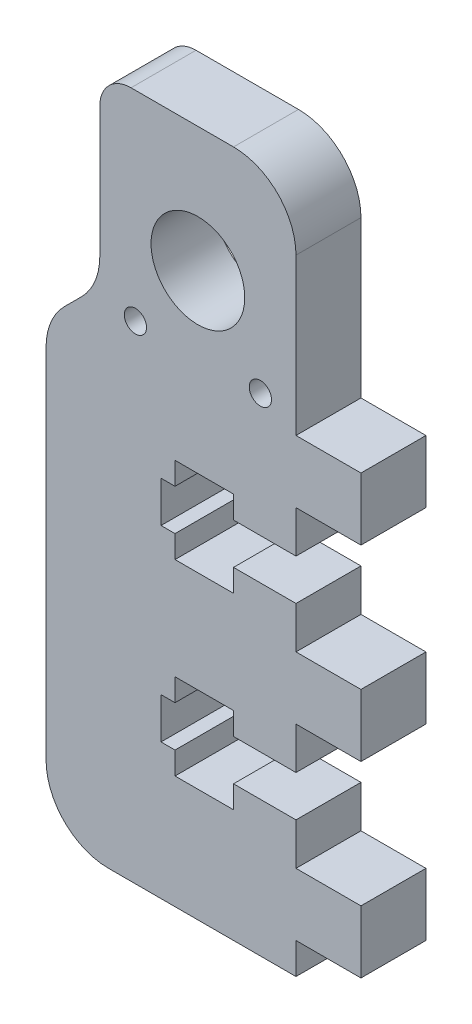
SolidWorks part; units mm, degrees
material "Acrylic (Blue)"
ref_plane "Front Plane" through (0, 0, 0) normal (0, 0, 1) x (1, 0, 0)
ref_plane "Top Plane" through (0, 0, 0) normal (0, 1, 0) x (1, 0, 0)
ref_plane "Right Plane" through (0, 0, 0) normal (1, 0, 0) x (0, 0, -1)
sketch "Sketch1" plane through (0, 0, 0) normal (0, 0, 1) x (1, 0, 0)
  line L0 (0, 0) -> (0, 69.85)
  line L1 (-9.9695, 57.15) -> (-9.9695, 129.438) construction
  line L2 (-19.939, 69.85) -> (0, 69.85)
  line L3 (0, 0) -> (-25.4, 0)
  line L4 (-25.4, 0) -> (-25.4, 45.339)
  line L6 (-19.939, 50.8) -> (-19.939, 69.85)
  line L7 (-19.939, 50.8) -> (-25.4, 45.339)
  circle A0 centre (-9.9695, 57.15) radius 4.7625
  circle A3 centre (-9.9695, 57.15) radius 8.6995 construction
  line B0 (0, 37.0078) -> (-6.35, 37.0078) construction
  line B1 (-6.35, 37.0078) -> (-6.35, 39.2938) construction
  line B2 (-6.35, 39.2938) -> (-12.2936, 39.2938) construction
  line B3 (-12.2936, 39.2938) -> (-12.2936, 37.0078) construction
  line B4 (-12.2936, 37.0078) -> (-13.716, 37.0078) construction
  line B5 (-13.716, 37.0078) -> (-13.716, 32.8422) construction
  line B6 (-13.716, 32.8422) -> (-12.2936, 32.8422) construction
  line B7 (-12.2936, 32.8422) -> (-12.2936, 30.5562) construction
  line B8 (-12.2936, 30.5562) -> (-6.35, 30.5562) construction
  line B9 (-6.35, 30.5562) -> (-6.35, 32.8422) construction
  line B10 (-6.35, 32.8422) -> (0, 32.8422) construction
  line B11 (0, 28.575) -> (6.604, 28.575) construction
  line B12 (6.604, 28.575) -> (6.604, 22.225) construction
  line B13 (6.604, 22.225) -> (0, 22.225) construction
  line B14 (0, 41.275) -> (6.604, 41.275) construction
  line B15 (6.604, 41.275) -> (6.604, 47.625) construction
  line B16 (6.604, 47.625) -> (0, 47.625) construction
  line B17 (6.604, 3.175) -> (0, 3.175) construction
  line B18 (0, 17.9578) -> (-6.35, 17.9578) construction
  line B19 (-6.35, 17.9578) -> (-6.35, 20.2438) construction
  line B20 (-6.35, 20.2438) -> (-12.2936, 20.2438) construction
  line B21 (-12.2936, 20.2438) -> (-12.2936, 17.9578) construction
  line B22 (-12.2936, 17.9578) -> (-13.716, 17.9578) construction
  line B23 (-13.716, 17.9578) -> (-13.716, 13.7922) construction
  line B24 (-13.716, 13.7922) -> (-12.2936, 13.7922) construction
  line B25 (-12.2936, 13.7922) -> (-12.2936, 11.5062) construction
  line B26 (-12.2936, 11.5062) -> (-6.35, 11.5062) construction
  line B27 (-6.35, 11.5062) -> (-6.35, 13.7922) construction
  line B28 (-6.35, 13.7922) -> (0, 13.7922) construction
  line B29 (0, 9.525) -> (6.604, 9.525) construction
  line B30 (6.604, 9.525) -> (6.604, 3.175) construction
  dimension "D3" = 9.525
  dimension "D4" = 57.15
  dimension "D5" = 17.399
  dimension "D2" = 1.27
  dimension "D6" = 25.4
  dimension "D1" = 69.85
  dimension "D7" = 6.731
  dimension "D8" = 1.27
  dimension "D9" = 19.05
  dimension "D10" = 45
  dimension "D11" = 3.175
sketch_block_instance "NUT_HOLE_2X-1"
sketch_block "NUT_HOLE_2X" parameters "D1"=6.35, "D2"=4.1656, "D3"=25.4, "D4"=6.604, "D5"=8.7376, "D6"=5.9436, "D7"=6.35, "D8"=20.32, "D9"=2
extrude "Boss-Extrude1" add sketch "Sketch1" along normal blind 6.604
sketch "Sketch2" plane through (0, 0, 6.604) normal (0, 0, 1) x (1, 0, 0)
  line L0 (-12.2936, 37.0078) -> (-13.716, 37.0078) construction
  line L1 (-12.2936, 39.2938) -> (-12.2936, 37.0078) construction
  line L2 (-6.35, 39.2938) -> (-12.2936, 39.2938) construction
  line L3 (-6.35, 37.0078) -> (-6.35, 39.2938) construction
  line L4 (0, 37.0078) -> (-6.35, 37.0078) construction
  line L5 (-6.35, 32.8422) -> (0, 32.8422) construction
  line L6 (-6.35, 30.5562) -> (-6.35, 32.8422) construction
  line L7 (-12.2936, 30.5562) -> (-6.35, 30.5562) construction
  line L8 (-12.2936, 32.8422) -> (-12.2936, 30.5562) construction
  line L9 (-13.716, 32.8422) -> (-12.2936, 32.8422) construction
  line L10 (-13.716, 37.0078) -> (-13.716, 32.8422) construction
  line L11 (-12.2936, 20.2438) -> (-12.2936, 17.9578) construction
  line L12 (-6.35, 20.2438) -> (-12.2936, 20.2438) construction
  line L13 (-12.2936, 17.9578) -> (-13.716, 17.9578) construction
  line L14 (-13.716, 17.9578) -> (-13.716, 13.7922) construction
  line L15 (-13.716, 13.7922) -> (-12.2936, 13.7922) construction
  line L16 (-12.2936, 13.7922) -> (-12.2936, 11.5062) construction
  line L17 (-12.2936, 11.5062) -> (-6.35, 11.5062) construction
  line L18 (-6.35, 11.5062) -> (-6.35, 13.7922) construction
  line L19 (-6.35, 13.7922) -> (0, 13.7922) construction
  line L20 (0, 17.9578) -> (-6.35, 17.9578) construction
  line L21 (-12.2936, 37.0078) -> (-13.716, 37.0078)
  line L22 (-12.2936, 39.2938) -> (-12.2936, 37.0078)
  line L23 (-6.35, 39.2938) -> (-12.2936, 39.2938)
  line L24 (-6.35, 37.0078) -> (-6.35, 39.2938)
  line L25 (0, 37.0078) -> (-6.35, 37.0078)
  line L26 (-6.35, 32.8422) -> (0, 32.8422)
  line L27 (-6.35, 30.5562) -> (-6.35, 32.8422)
  line L28 (-12.2936, 30.5562) -> (-6.35, 30.5562)
  line L29 (-12.2936, 32.8422) -> (-12.2936, 30.5562)
  line L30 (-13.716, 32.8422) -> (-12.2936, 32.8422)
  line L31 (-13.716, 37.0078) -> (-13.716, 32.8422)
  line L32 (-12.2936, 20.2438) -> (-12.2936, 17.9578)
  line L33 (-6.35, 20.2438) -> (-12.2936, 20.2438)
  line L34 (-12.2936, 17.9578) -> (-13.716, 17.9578)
  line L35 (-13.716, 17.9578) -> (-13.716, 13.7922)
  line L36 (-13.716, 13.7922) -> (-12.2936, 13.7922)
  line L37 (-12.2936, 13.7922) -> (-12.2936, 11.5062)
  line L38 (-12.2936, 11.5062) -> (-6.35, 11.5062)
  line L39 (-6.35, 11.5062) -> (-6.35, 13.7922)
  line L40 (-6.35, 13.7922) -> (0, 13.7922)
  line L41 (0, 17.9578) -> (-6.35, 17.9578)
  line L42 (0, 37.0078) -> (0, 32.8422)
  line L43 (0, 17.9578) -> (0, 13.7922)
  line L45 (-6.35, 17.9578) -> (-6.35, 20.2438) construction
  line L46 (-6.35, 17.9578) -> (-6.35, 20.2438)
extrude "Cut-Extrude1" cut sketch "Sketch2" against normal through all
sketch "Sketch3" plane through (0, 0, 6.604) normal (0, 0, 1) x (1, 0, 0)
  line L0 (6.604, 47.625) -> (0, 47.625) construction
  line L1 (6.604, 41.275) -> (6.604, 47.625) construction
  line L2 (0, 41.275) -> (6.604, 41.275) construction
  line L3 (0, 28.575) -> (6.604, 28.575) construction
  line L4 (6.604, 28.575) -> (6.604, 22.225) construction
  line L5 (6.604, 22.225) -> (0, 22.225) construction
  line L6 (0, 9.525) -> (6.604, 9.525) construction
  line L7 (6.604, 9.525) -> (6.604, 3.175) construction
  line L8 (6.604, 3.175) -> (0, 3.175) construction
  line L9 (6.604, 47.625) -> (0, 47.625)
  line L10 (6.604, 41.275) -> (6.604, 47.625)
  line L11 (0, 41.275) -> (6.604, 41.275)
  line L12 (0, 28.575) -> (6.604, 28.575)
  line L13 (6.604, 28.575) -> (6.604, 22.225)
  line L14 (6.604, 22.225) -> (0, 22.225)
  line L15 (0, 9.525) -> (6.604, 9.525)
  line L16 (6.604, 9.525) -> (6.604, 3.175)
  line L17 (6.604, 3.175) -> (0, 3.175)
  line L18 (0, 47.625) -> (0, 41.275)
  line L19 (0, 28.575) -> (0, 22.225)
  line L20 (0, 9.525) -> (0, 3.175)
extrude "Boss-Extrude2" add sketch "Sketch3" against normal up to surface (6.604 mm away) up to face at (-9.823, 28.1813, 0)
fillet "Fillet1" radius 6.35 4 edges at (-25.4, 0, 3.302) (0, 69.85, 3.302) (-25.4, 45.339, 3.302) (-19.939, 50.8, 3.302)
fillet "Fillet2" radius 3.175 1 edges at (-19.939, 69.85, 3.302)
hole_wizard "#4-40 Tapped Hole1" positions "Sketch5" profile "Sketch4" tap size "#4-40" standard "ANSI Inch"
sketch "Sketch5" plane through (0, 0, 6.604) normal (0, 0, 1) x (1, 0, 0)
  line L0 (-3.6195, 49.53) -> (-16.3195, 49.53) construction
  line L3 (-6.35, 69.85) -> (-16.764, 69.85) construction
  line L4 (-9.9695, 49.53) -> (-9.9695, 57.15) construction
  point P0 (-3.6195, 49.53)
  point P2 (-16.3195, 49.53)
  dimension "D1" = 20.32
  dimension "D2" = 12.7
sketch "Sketch4" plane through (-3.6195, 49.53, 6.604) normal (1, 0, 0) x (0, -1, 0)
  line L0 (0, 0) -> (0, 8.2738)
  line L1 (0, 8.2738) -> (1.1303, 7.5946)
  line L2 (1.1303, 7.5946) -> (1.1303, 0)
  line L5 (1.1303, 0) -> (0, 0)
  line L10 (0, 8.2738) -> (-1.1303, 7.5946) construction
  line L11 (0, -6.35) -> (0, 107.95) construction
  dimension "Tap Drill Dia." = 2.2606
  dimension "Tap Drill Depth" = 7.5946
  dimension "Drill Angle" = 118
other "Move Face1" [suppressed] parameters "D1"=0.0508
